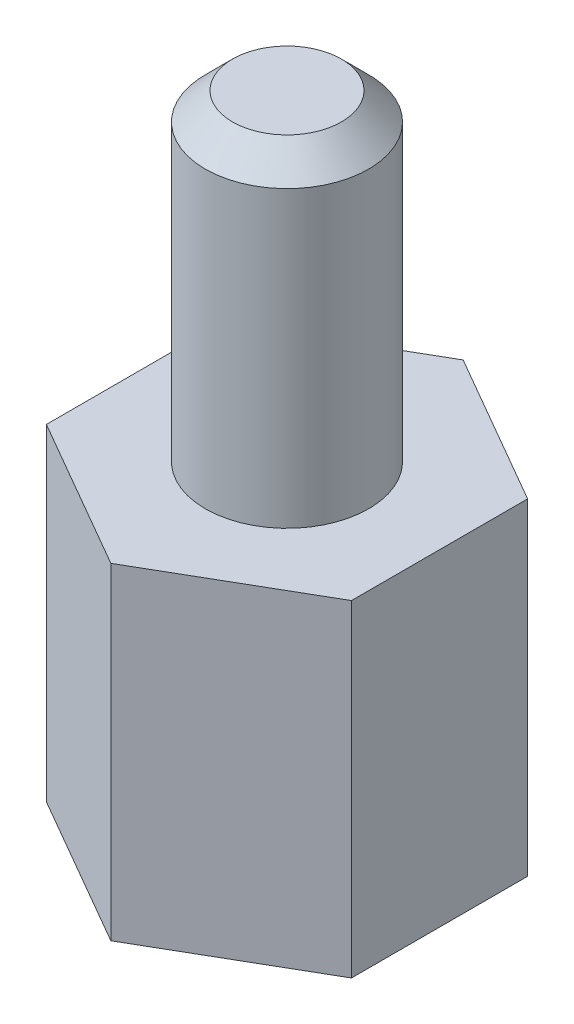
SolidWorks part; units mm, degrees
ref_plane "Front Plane" through (0, 0, 0) normal (0, 0, 1) x (1, 0, 0)
ref_plane "Top Plane" through (0, 0, 0) normal (0, 1, 0) x (1, 0, 0)
ref_plane "Right Plane" through (0, 0, 0) normal (1, 0, 0) x (0, 0, -1)
sketch "Sketch1" plane through (0, 0, 0) normal (0, 1, 0) x (1, 0, 0)
  line L1 (0, -3.2332) -> (2.8, -1.6166)
  line L2 (2.8, -1.6166) -> (2.8, 1.6166)
  line L3 (2.8, 1.6166) -> (0, 3.2332)
  line L4 (0, 3.2332) -> (-2.8, 1.6166)
  line L5 (-2.8, 1.6166) -> (-2.8, -1.6166)
  line L6 (-2.8, -1.6166) -> (0, -3.2332)
  circle A0 centre (0, 0) radius 2.8 construction
  dimension "D1" = 5.6
extrude "Boss-Extrude1" add sketch "Sketch1" along normal blind 6
sketch "Sketch2" plane through (0, 6, 0) normal (0, 1, 0) x (1, 0, 0)
  circle A0 centre (0, 0) radius 1.5
  dimension "D1" = 3
extrude "Boss-Extrude2" add sketch "Sketch2" along normal blind 5.9
sketch "Sketch3" plane through (0, 0, 0) normal (0, -1, 0) x (1, 0, 0)
  circle A0 centre (0, 0) radius 1.5
  dimension "D1" = 3
extrude "Cut-Extrude1" cut sketch "Sketch3" against normal offset from surface (4 mm away) 2 up to face at (0, 6, 1.5)
chamfer "Chamfer1" distance 0.5 angle 45 1 edges at (0, 11.9, 1.5)
